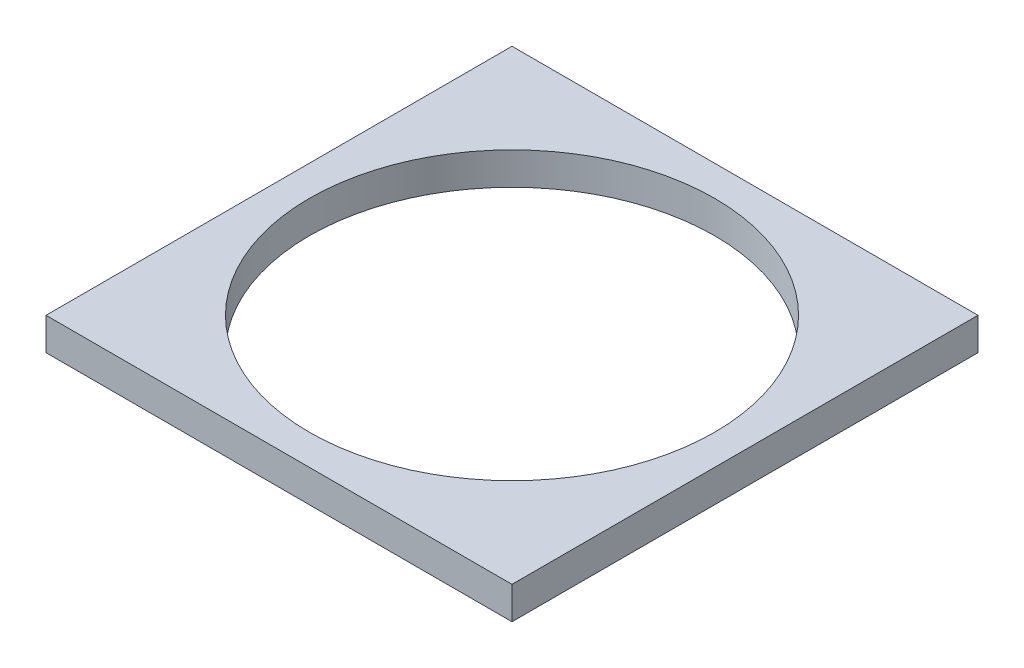
SolidWorks part; units mm, degrees
ref_plane "Front Plane" through (0, 0, 0) normal (0, 0, 1) x (1, 0, 0)
ref_plane "Top Plane" through (0, 0, 0) normal (0, 1, 0) x (1, 0, 0)
ref_plane "Right Plane" through (0, 0, 0) normal (1, 0, 0) x (0, 0, -1)
sketch "Sketch1" plane through (0, 0, 0) normal (0, 1, 0) x (1, 0, 0)
  line L1 (-8.9444, 8.8075) -> (2.5556, 8.8075)
  line L2 (-8.9444, 8.8075) -> (-8.9444, -2.6925)
  line L3 (-8.9444, -2.6925) -> (2.5556, -2.6925)
  line L4 (2.5556, 8.8075) -> (2.5556, -2.6925)
  line L5 (-3.1944, -2.6925) -> (-3.1944, 8.8075) construction
  line L6 (-8.9444, 3.0575) -> (2.5556, 3.0575) construction
  circle A0 centre (-3.1944, 3.0575) radius 5
  point P0 (-3.1944, 3.0575)
  dimension "D3" = 10
  dimension "D1" = 11.5
  dimension "D2" = 11.5
extrude "Boss-Extrude1" add sketch "Sketch1" along normal blind 0.8
